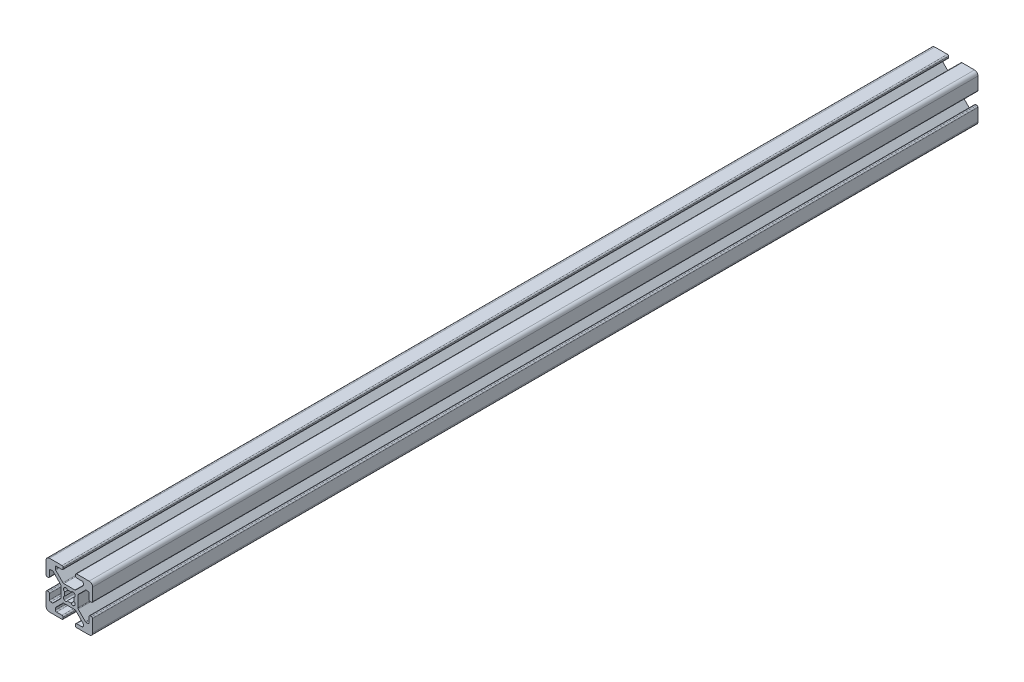
SolidWorks part; units mm, degrees
ref_plane "Front Plane" through (0, 0, 0) normal (0, 0, 1) x (1, 0, 0)
ref_plane "Top Plane" through (0, 0, 0) normal (0, 1, 0) x (1, 0, 0)
ref_plane "Right Plane" through (0, 0, 0) normal (1, 0, 0) x (0, 0, -1)
sketch "Sketch1" plane through (0, 0, 0) normal (0, 0, 1) x (1, 0, 0)
  line L0 (-5.0323, -0.3411) -> (-5.5163, -0.3411)
  line L1 (-6.0243, 0.1669) -> (-6.0243, 2.5159)
  line L2 (-4.5243, 0.1669) -> (-4.5243, 5.5289)
  line L3 (-10.8693, -5.355) -> (-10.8693, -0.5871)
  line L4 (-7.2582, 3.0239) -> (-6.5323, 3.0239)
  line L5 (-7.6174, 2.8752) -> (-10.7205, -0.2279)
  line L6 (-5.0323, -5.6011) -> (-5.5163, -5.6011)
  line L7 (-4.5243, -6.1091) -> (-4.5243, -11.4711)
  line L8 (-6.0243, -6.1091) -> (-6.0243, -8.4581)
  line L9 (-7.2582, -8.9661) -> (-6.5323, -8.9661)
  line L10 (-7.6174, -8.8173) -> (-10.7205, -5.7142)
  line L11 (-12.3994, -5.2756) -> (-12.2198, -5.096)
  line L12 (-17.1543, 6.5209) -> (-17.1543, 6.0369)
  line L13 (-17.6623, 7.0289) -> (-23.0243, 7.0289)
  line L14 (-17.6623, 5.5289) -> (-20.0113, 5.5289)
  line L15 (-12.1404, 0.6839) -> (-16.9082, 0.6839)
  line L16 (-20.5193, 4.295) -> (-20.5193, 5.0209)
  line L17 (-20.3705, 3.9358) -> (-17.2674, 0.8327)
  line L18 (-11.8943, 6.5209) -> (-11.8943, 6.0369)
  line L19 (-11.3863, 7.0289) -> (-6.0243, 7.0289)
  line L20 (-11.3863, 5.5289) -> (-9.0373, 5.5289)
  line L21 (-8.5293, 4.295) -> (-8.5293, 5.0209)
  line L22 (-8.6781, 3.9358) -> (-11.7812, 0.8327)
  line L23 (-12.2198, -0.8462) -> (-12.3994, -0.6666)
  line L24 (-24.0163, -5.6011) -> (-23.5323, -5.6011)
  line L25 (-24.5243, -6.1091) -> (-24.5243, -11.4711)
  line L26 (-23.0243, -6.1091) -> (-23.0243, -8.4581)
  line L27 (-18.1793, -0.5871) -> (-18.1793, -5.355)
  line L28 (-21.7904, -8.9661) -> (-22.5163, -8.9661)
  line L29 (-21.4312, -8.8173) -> (-18.3281, -5.7142)
  line L30 (-24.0163, -0.3411) -> (-23.5323, -0.3411)
  line L31 (-24.5243, 0.1669) -> (-24.5243, 5.5289)
  line L32 (-23.0243, 0.1669) -> (-23.0243, 2.5159)
  line L33 (-21.7904, 3.0239) -> (-22.5163, 3.0239)
  line L34 (-21.4312, 2.8752) -> (-18.3281, -0.2279)
  line L35 (-16.6492, -0.6666) -> (-16.8288, -0.8462)
  line L36 (-11.8943, -12.4631) -> (-11.8943, -11.9791)
  line L37 (-11.3863, -12.9711) -> (-6.0243, -12.9711)
  line L38 (-11.3863, -11.4711) -> (-9.0373, -11.4711)
  line L39 (-16.9082, -6.6261) -> (-12.1404, -6.6261)
  line L40 (-8.5293, -10.2371) -> (-8.5293, -10.9631)
  line L41 (-8.6781, -9.8779) -> (-11.7812, -6.7748)
  line L42 (-17.1543, -12.4631) -> (-17.1543, -11.9791)
  line L43 (-17.6623, -12.9711) -> (-23.0243, -12.9711)
  line L44 (-17.6623, -11.4711) -> (-20.0113, -11.4711)
  line L45 (-20.5193, -10.2371) -> (-20.5193, -10.9631)
  line L46 (-20.3705, -9.8779) -> (-17.2674, -6.7748)
  line L47 (-16.8288, -5.096) -> (-16.6492, -5.2756)
  arc A0 (-15.3283, -4.9062) -> (-13.7203, -4.9062) centre (-14.5243, -2.9711) ccw
  arc A1 (-6.0243, 2.5159) -> (-6.5323, 3.0239) centre (-6.5323, 2.5159) ccw
  arc A2 (-7.2582, 3.0239) -> (-7.6174, 2.8752) centre (-7.2582, 2.5159) ccw
  arc A3 (-10.7205, -0.2279) -> (-10.8693, -0.5871) centre (-10.3613, -0.5871) ccw
  arc A4 (-10.8693, -5.355) -> (-10.7205, -5.7142) centre (-10.3613, -5.355) ccw
  arc A5 (-7.6174, -8.8173) -> (-7.2582, -8.9661) centre (-7.2582, -8.4581) ccw
  arc A6 (-6.5323, -8.9661) -> (-6.0243, -8.4581) centre (-6.5323, -8.4581) ccw
  arc A7 (-5.5163, -5.6011) -> (-6.0243, -6.1091) centre (-5.5163, -6.1091) ccw
  arc A8 (-4.5243, -6.1091) -> (-5.0323, -5.6011) centre (-5.0323, -6.1091) ccw
  arc A9 (-5.0323, -0.3411) -> (-4.5243, 0.1669) centre (-5.0323, 0.1669) ccw
  arc A10 (-6.0243, 0.1669) -> (-5.5163, -0.3411) centre (-5.5163, 0.1669) ccw
  arc A11 (-13.7203, -4.9062) -> (-12.3994, -5.2756) centre (-12.9559, -4.7191) ccw
  arc A12 (-12.2198, -5.096) -> (-12.5892, -3.775) centre (-12.7763, -4.5395) ccw
  arc A13 (-17.1543, 6.5209) -> (-17.6623, 7.0289) centre (-17.6623, 6.5209) ccw
  arc A14 (-17.6623, 5.5289) -> (-17.1543, 6.0369) centre (-17.6623, 6.0369) ccw
  arc A15 (-12.5892, -3.775) -> (-12.5892, -2.1671) centre (-14.5243, -2.9711) ccw
  arc A16 (-17.2674, 0.8327) -> (-16.9082, 0.6839) centre (-16.9082, 1.1919) ccw
  arc A17 (-20.0113, 5.5289) -> (-20.5193, 5.0209) centre (-20.0113, 5.0209) ccw
  arc A18 (-20.5193, 4.295) -> (-20.3705, 3.9358) centre (-20.0113, 4.295) ccw
  arc A19 (-11.8943, 6.0369) -> (-11.3863, 5.5289) centre (-11.3863, 6.0369) ccw
  arc A20 (-11.3863, 7.0289) -> (-11.8943, 6.5209) centre (-11.3863, 6.5209) ccw
  arc A21 (-8.5293, 5.0209) -> (-9.0373, 5.5289) centre (-9.0373, 5.0209) ccw
  arc A22 (-8.6781, 3.9358) -> (-8.5293, 4.295) centre (-9.0373, 4.295) ccw
  arc A23 (-12.1404, 0.6839) -> (-11.7812, 0.8327) centre (-12.1404, 1.1919) ccw
  arc A24 (-12.5892, -2.1671) -> (-12.2198, -0.8462) centre (-12.7763, -1.4027) ccw
  arc A25 (-12.3994, -0.6666) -> (-13.7203, -1.0359) centre (-12.9559, -1.223) ccw
  arc A26 (-24.0163, -5.6011) -> (-24.5243, -6.1091) centre (-24.0163, -6.1091) ccw
  arc A27 (-23.0243, -6.1091) -> (-23.5323, -5.6011) centre (-23.5323, -6.1091) ccw
  arc A28 (-13.7203, -1.0359) -> (-15.3283, -1.0359) centre (-14.5243, -2.9711) ccw
  arc A29 (-18.3281, -5.7142) -> (-18.1793, -5.355) centre (-18.6873, -5.355) ccw
  arc A30 (-23.0243, -8.4581) -> (-22.5163, -8.9661) centre (-22.5163, -8.4581) ccw
  arc A31 (-21.7904, -8.9661) -> (-21.4312, -8.8173) centre (-21.7904, -8.4581) ccw
  arc A32 (-23.5323, -0.3411) -> (-23.0243, 0.1669) centre (-23.5323, 0.1669) ccw
  arc A33 (-24.5243, 0.1669) -> (-24.0163, -0.3411) centre (-24.0163, 0.1669) ccw
  arc A34 (-22.5163, 3.0239) -> (-23.0243, 2.5159) centre (-22.5163, 2.5159) ccw
  arc A35 (-21.4312, 2.8752) -> (-21.7904, 3.0239) centre (-21.7904, 2.5159) ccw
  arc A36 (-18.1793, -0.5871) -> (-18.3281, -0.2279) centre (-18.6873, -0.5871) ccw
  arc A37 (-15.3283, -1.0359) -> (-16.6492, -0.6666) centre (-16.0927, -1.223) ccw
  arc A38 (-16.8288, -0.8462) -> (-16.4594, -2.1671) centre (-16.2723, -1.4027) ccw
  arc A39 (-11.8943, -12.4631) -> (-11.3863, -12.9711) centre (-11.3863, -12.4631) ccw
  arc A40 (-11.3863, -11.4711) -> (-11.8943, -11.9791) centre (-11.3863, -11.9791) ccw
  arc A41 (-16.4594, -2.1671) -> (-16.4594, -3.775) centre (-14.5243, -2.9711) ccw
  arc A42 (-11.7812, -6.7748) -> (-12.1404, -6.6261) centre (-12.1404, -7.1341) ccw
  arc A43 (-9.0373, -11.4711) -> (-8.5293, -10.9631) centre (-9.0373, -10.9631) ccw
  arc A44 (-8.5293, -10.2371) -> (-8.6781, -9.8779) centre (-9.0373, -10.2371) ccw
  arc A45 (-17.1543, -11.9791) -> (-17.6623, -11.4711) centre (-17.6623, -11.9791) ccw
  arc A46 (-17.6623, -12.9711) -> (-17.1543, -12.4631) centre (-17.6623, -12.4631) ccw
  arc A47 (-20.5193, -10.9631) -> (-20.0113, -11.4711) centre (-20.0113, -10.9631) ccw
  arc A48 (-20.3705, -9.8779) -> (-20.5193, -10.2371) centre (-20.0113, -10.2371) ccw
  arc A49 (-16.9082, -6.6261) -> (-17.2674, -6.7748) centre (-16.9082, -7.1341) ccw
  arc A50 (-16.4594, -3.775) -> (-16.8288, -5.096) centre (-16.2723, -4.5395) ccw
  arc A51 (-16.6492, -5.2756) -> (-15.3283, -4.9062) centre (-16.0927, -4.7191) ccw
  arc A52 (-4.5243, 5.5289) -> (-6.0243, 7.0289) centre (-6.0243, 5.5289) ccw
  arc A53 (-6.0243, -12.9711) -> (-4.5243, -11.4711) centre (-6.0243, -11.4711) ccw
  arc A54 (-24.5243, -11.4711) -> (-23.0243, -12.9711) centre (-23.0243, -11.4711) ccw
  arc A55 (-23.0243, 7.0289) -> (-24.5243, 5.5289) centre (-23.0243, 5.5289) ccw
extrude "Extrude1" add sketch "Sketch1" along normal blind 380
